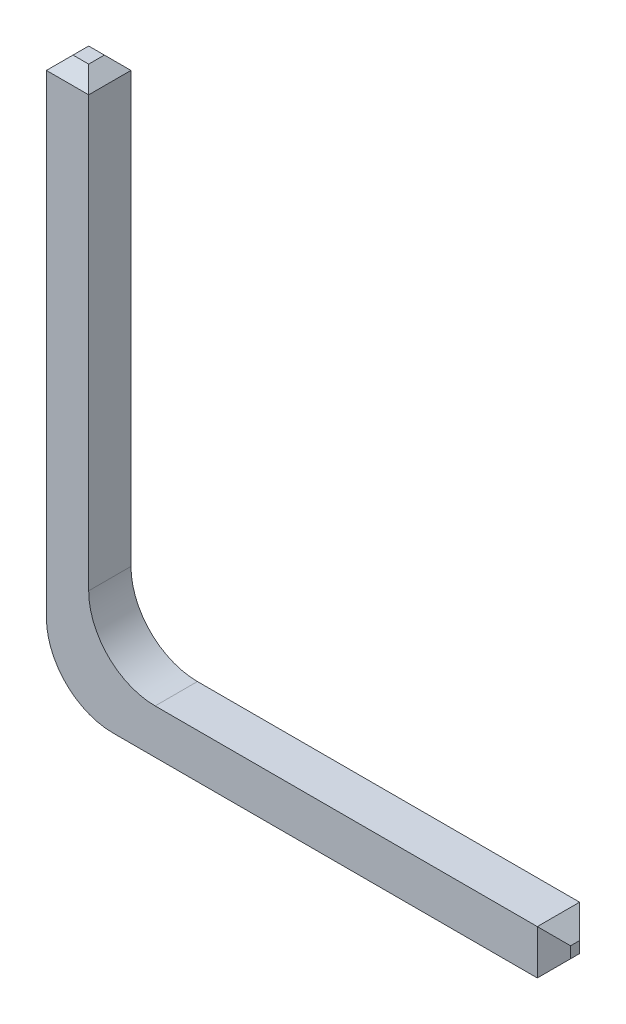
SolidWorks part; units mm, degrees
ref_plane "Alzado" through (0, 0, 0) normal (0, 0, 1) x (1, 0, 0)
ref_plane "Planta" through (0, 0, 0) normal (0, 1, 0) x (1, 0, 0)
ref_plane "Vista lateral" through (0, 0, 0) normal (1, 0, 0) x (0, 0, -1)
sketch "pin_drawing" plane through (0, 0, 0) normal (0, 1, 0) x (1, 0, 0)
  line L1 (0, 0) -> (0.636, 0)
  line L2 (0, 0) -> (0, -0.636)
  line L3 (0, -0.636) -> (0.636, -0.636)
  line L4 (0.636, 0) -> (0.636, -0.636)
extrude "pin" add sketch "pin_drawing" along normal blind 11.54
chamfer "Chamfer2" distance 0.2 angle 45 8 edges at (0, 0, 0.318) (0.318, 0, 0) (0.636, 0, 0.318) (0.318, 0, 0.636) (0.318, 11.54, 0.636) (0.636, 11.54, 0.318) (0.318, 11.54, 0) (0, 11.54, 0.318)
sketch "Sketch1" plane through (0, 0, 0) normal (0, 0, -1) x (-1, 0, 0)
  line L0 (-0.636, 3.2071) -> (-7.636, 3.2071)
  line L1 (-0.636, 11.34) -> (-0.636, 0.2) construction
  line L2 (-7.636, 3.2071) -> (-7.636, 3.8771)
  line L3 (-0.636, 3.2071) -> (-0.636, 3.8771)
  line L5 (-7.636, 3.8771) -> (-0.636, 3.8771)
  dimension "D1" = 0.67
  dimension "D2" = 7
extrude "Boss-Extrude1" add sketch "Sketch1" against normal up to surface (0.636 mm away) up to face at (0.318, 5.77, 0.636)
chamfer "Chamfer3" distance 0.25 angle 45 4 edges at (7.636, 3.8771, 0.318) (7.636, 3.5421, 0.636) (7.636, 3.5421, 0) (7.636, 3.2071, 0.318)
sketch "Sketch2" plane through (0, 0, 0) normal (0, 0, -1) x (-1, 0, 0)
  line L0 (-0.636, 3.2071) -> (0, 3.2071)
  line L1 (0, 11.34) -> (0, 0.2) construction
  line L2 (0, 3.2071) -> (0, -0.4333)
  line L3 (0, -0.4333) -> (-0.636, -0.4333)
  line L4 (-0.636, -0.4333) -> (-0.636, 3.2071)
  line L5 (-0.636, 3.2071) -> (-0.636, 0.2) construction
extrude "Cut-Extrude1" cut sketch "Sketch2" against normal up to surface (0.636 mm away) up to face at (2.1645, 5.3104, 0.636)
fillet "Fillet1" radius 1 2 edges at (0, 3.2071, 0.318)
